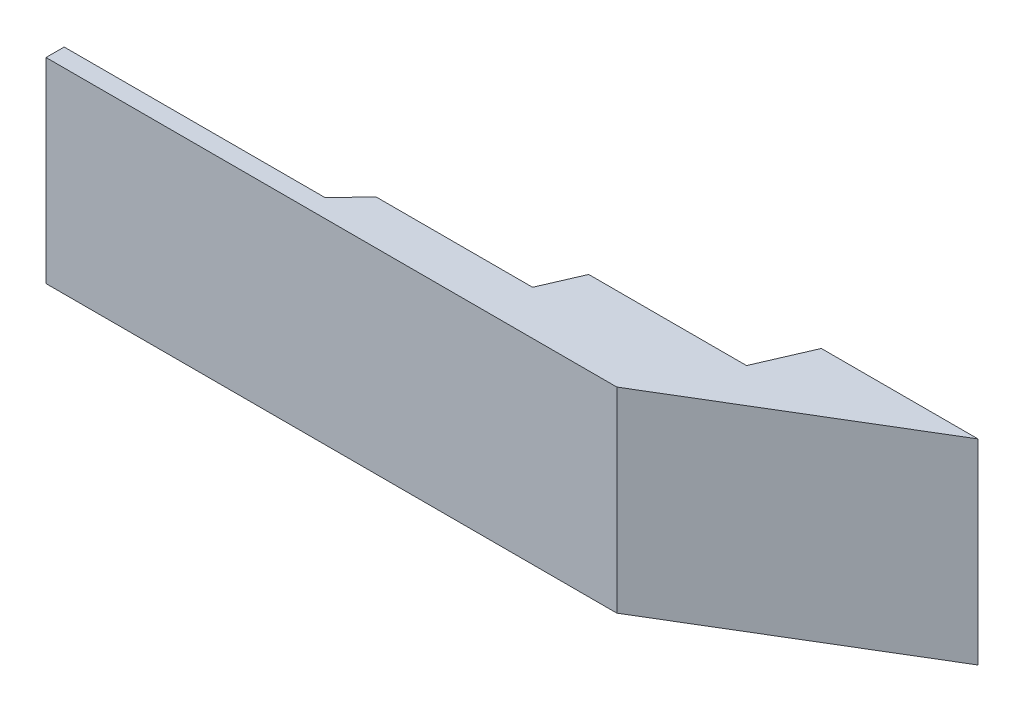
SolidWorks part; units mm, degrees
ref_plane "Front Plane" through (0, 0, 0) normal (0, 0, 1) x (1, 0, 0)
ref_plane "Top Plane" through (0, 0, 0) normal (0, 1, 0) x (1, 0, 0)
ref_plane "Right Plane" through (0, 0, 0) normal (1, 0, 0) x (0, 0, -1)
sketch "Sketch1" plane through (0, 0, 0) normal (0, 1, 0) x (1, 0, 0)
  line L0 (-2629.1045, 0) -> (-629.1045, 0)
  line L1 (-629.1045, 0) -> (-441.0448, 200)
  line L2 (-441.0448, 200) -> (29.1045, 200)
  line L3 (29.1045, 200) -> (758.9552, 200)
  line L4 (758.9552, 200) -> (888.806, 500)
  line L5 (888.806, 500) -> (2097.7612, 500)
  line L6 (2097.7612, 500) -> (2270.8955, 900)
  line L7 (2270.8955, 900) -> (3470.8955, 900)
  line L8 (-2629.1045, 0) -> (-2629.1045, -139.2804)
  line L9 (-2629.1045, -139.2804) -> (1743.3758, -139.2804)
  line L10 (1743.3758, -139.2804) -> (3470.8955, 900)
  point P3 (2097.7612, 73.9188)
  dimension "D1" = 1200
  dimension "D2" = 200
  dimension "D3" = 300
  dimension "D4" = 1200
  dimension "D5" = 400
  dimension "D6" = 2000
extrude "Boss-Extrude1" add sketch "Sketch1" along normal blind 1500
